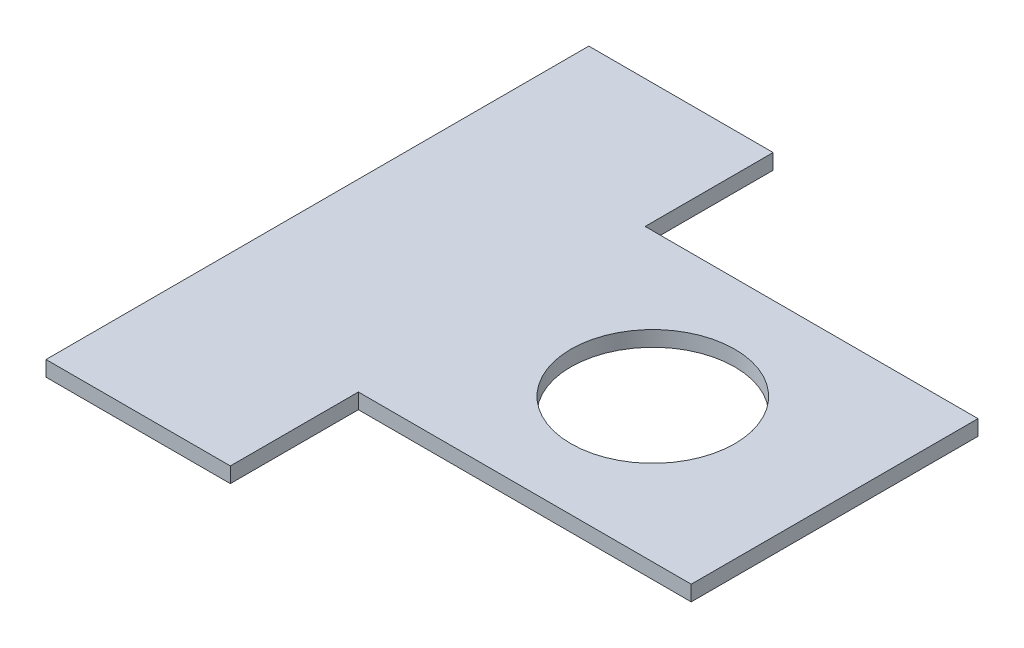
SolidWorks part; units mm, degrees
ref_plane "Front Plane" through (0, 0, 0) normal (0, 0, 1) x (1, 0, 0)
ref_plane "Top Plane" through (0, 0, 0) normal (0, 1, 0) x (1, 0, 0)
ref_plane "Right Plane" through (0, 0, 0) normal (1, 0, 0) x (0, 0, -1)
sketch "Sketch1" plane through (0, 0, 0) normal (0, 1, 0) x (1, 0, 0)
  line L1 (0, -53) -> (0, 53)
  line L2 (0, 53) -> (36, 53)
  line L3 (36, 53) -> (36, 28)
  line L4 (36, 28) -> (101, 28)
  line L5 (101, 28) -> (101, -28)
  line L6 (36, -28) -> (101, -28)
  line L7 (36, -53) -> (36, -28)
  line L8 (0, -53) -> (36, -53)
  line L9 (36, 28) -> (65.5, 28)
  line L10 (65.5, 28) -> (65.5, 0)
  circle A0 centre (65.5, 0) radius 16
extrude "Boss-Extrude1" add sketch "Sketch1" along normal blind 3
